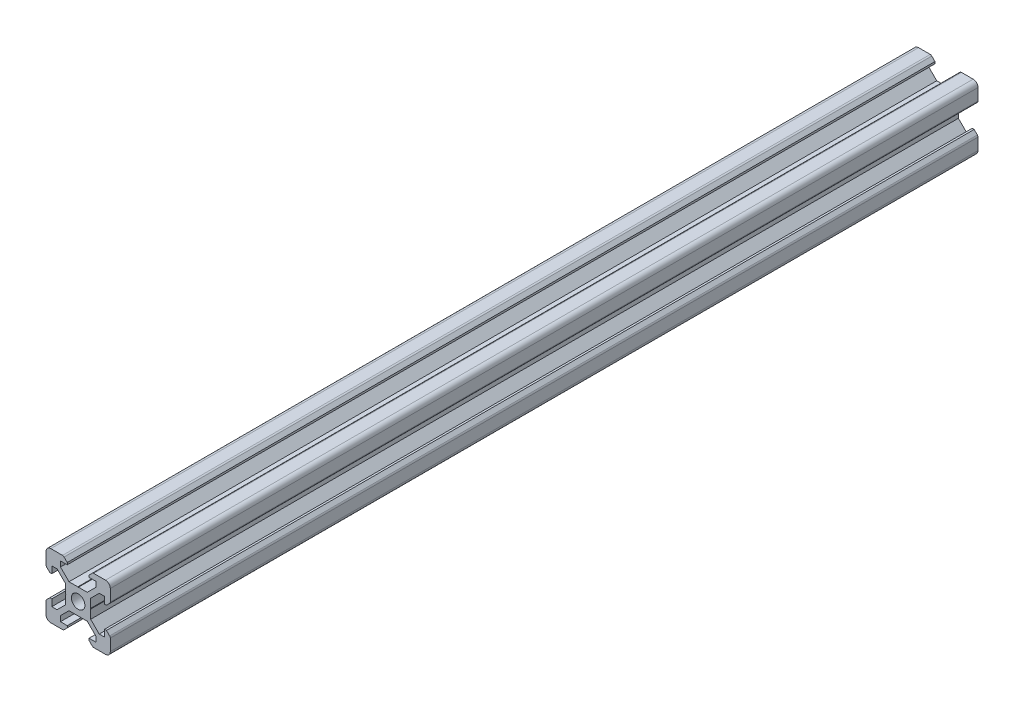
SolidWorks part; units mm, degrees
ref_plane "Front" through (0, 0, 0) normal (0, 0, 1) x (1, 0, 0)
ref_plane "Top" through (0, 0, 0) normal (0, 1, 0) x (1, 0, 0)
ref_plane "Right" through (0, 0, 0) normal (1, 0, 0) x (0, 0, -1)
sketch "Sketch1" plane through (0, 0, 0) normal (0, 0, 1) x (1, 0, 0)
  line L0 (-8.5, 10) -> (-10, 8.5) construction
  line L1 (-8.5, 10) -> (-4.8628, 10)
  line L2 (-10, 8.5) -> (-10, 4.8628)
  line L3 (-8.5, -10) -> (-4.8628, -10)
  line L4 (10, 8.5) -> (10, 4.8628)
  line L5 (-10, 10) -> (10, -10) construction
  line L6 (-10, -10) -> (10, 10) construction
  line L7 (-5.5, -8.2) -> (-3.3865, -8.2)
  line L8 (-8.2, -5.5) -> (-8.2, -3.3865)
  line L9 (-5.5, 8.2) -> (-3.3865, 8.2)
  line L10 (8.2, -5.5) -> (8.2, -3.3865)
  line L11 (-3.9005, 2.8395) -> (-6.561, 5.5)
  line L12 (-6.561, 5.5) -> (-8.2, 5.5)
  line L13 (-2.8395, -3.9005) -> (-0.1, -3.9005)
  line L14 (-3.9005, -2.8395) -> (-3.9005, -0.1)
  line L15 (-2.8395, 3.9005) -> (-0.1, 3.9005)
  line L16 (3.9005, -2.8395) -> (3.9005, -0.1)
  line L17 (-8.2, 3.3865) -> (-8.81, 3.3865)
  line L18 (-8.81, 3.3865) -> (-9.7976, 4.3741)
  line L19 (8.5, 10) -> (10, 8.5) construction
  line L20 (-2.8395, 3.9005) -> (-5.5, 6.561)
  line L21 (-5.5, 6.561) -> (-5.5, 8.2)
  line L22 (-3.3865, 8.2) -> (-3.3865, 8.81)
  line L23 (-3.3865, 8.81) -> (-4.3741, 9.7976)
  line L24 (0, 24.069) -> (0, -33.8154) construction
  line L25 (3.3865, 8.81) -> (4.3741, 9.7976)
  line L26 (3.3865, 8.2) -> (3.3865, 8.81)
  line L27 (5.5, 6.561) -> (5.5, 8.2)
  line L28 (2.8395, 3.9005) -> (5.5, 6.561)
  line L29 (3.3865, 8.2) -> (5.5, 8.2)
  line L30 (4.8628, 10) -> (8.5, 10)
  line L31 (-0.1, 3.9005) -> (0, 3.8005)
  line L32 (0.1, 3.9005) -> (0, 3.8005)
  line L33 (0.1, 3.9005) -> (2.8395, 3.9005)
  line L34 (25.9287, 0) -> (-28.3459, 0) construction
  line L35 (-0.1, -3.9005) -> (0, -3.8005)
  line L36 (0.1, -3.9005) -> (0, -3.8005)
  line L37 (0.1, -3.9005) -> (2.8395, -3.9005)
  line L38 (-3.9005, 0.1) -> (-3.8005, 0)
  line L39 (-3.8005, 0) -> (-3.9005, -0.1)
  line L40 (-3.9005, 0.1) -> (-3.9005, 2.8395)
  line L41 (3.9005, 0.1) -> (3.8005, 0)
  line L42 (3.8005, 0) -> (3.9005, -0.1)
  line L43 (3.9005, 0.1) -> (3.9005, 2.8395)
  line L44 (8.81, 3.3865) -> (9.7976, 4.3741)
  line L45 (8.2, 3.3865) -> (8.81, 3.3865)
  line L46 (6.561, 5.5) -> (8.2, 5.5)
  line L47 (3.9005, 2.8395) -> (6.561, 5.5)
  line L48 (2.8395, -3.9005) -> (5.5, -6.561)
  line L49 (3.9005, -2.8395) -> (6.561, -5.5)
  line L50 (-2.8395, -3.9005) -> (-5.5, -6.561)
  line L51 (-3.9005, -2.8395) -> (-6.561, -5.5)
  line L52 (6.561, -5.5) -> (8.2, -5.5)
  line L53 (-6.561, -5.5) -> (-8.2, -5.5)
  line L54 (-8.81, -3.3865) -> (-9.7976, -4.3741)
  line L55 (-8.2, -3.3865) -> (-8.81, -3.3865)
  line L56 (8.81, -3.3865) -> (9.7976, -4.3741)
  line L57 (8.2, -3.3865) -> (8.81, -3.3865)
  line L58 (8.2, 3.3865) -> (8.2, 5.5)
  line L59 (10, -4.8628) -> (10, -8.5)
  line L60 (-8.2, 3.3865) -> (-8.2, 5.5)
  line L61 (-10, -4.8628) -> (-10, -8.5)
  line L62 (-3.3865, -8.81) -> (-4.3741, -9.7976)
  line L63 (-3.3865, -8.2) -> (-3.3865, -8.81)
  line L64 (3.3865, -8.81) -> (4.3741, -9.7976)
  line L65 (3.3865, -8.2) -> (3.3865, -8.81)
  line L66 (-5.5, -6.561) -> (-5.5, -8.2)
  line L67 (5.5, -6.561) -> (5.5, -8.2)
  line L68 (3.3865, -8.2) -> (5.5, -8.2)
  line L69 (4.8628, -10) -> (8.5, -10)
  circle A0 centre (0, 0) radius 2.1
  arc A1 (-8.5, 10) -> (-10, 8.5) centre (-8.5, 8.5) ccw
  arc A2 (10, 8.5) -> (8.5, 10) centre (8.5, 8.5) ccw
  arc A3 (-4.3741, 9.7976) -> (-4.8628, 10) centre (-4.8628, 9.3088) ccw
  arc A4 (4.8628, 10) -> (4.3741, 9.7976) centre (4.8628, 9.3088) ccw
  arc A5 (-8.5, -10) -> (-10, -8.5) centre (-8.5, -8.5) cw
  arc A6 (9.7976, 4.3741) -> (10, 4.8628) centre (9.3088, 4.8628) ccw
  arc A7 (-10, 4.8628) -> (-9.7976, 4.3741) centre (-9.3088, 4.8628) ccw
  arc A8 (-10, -4.8628) -> (-9.7976, -4.3741) centre (-9.3088, -4.8628) cw
  arc A9 (9.7976, -4.3741) -> (10, -4.8628) centre (9.3088, -4.8628) cw
  arc A10 (10, -8.5) -> (8.5, -10) centre (8.5, -8.5) cw
  arc A11 (-4.3741, -9.7976) -> (-4.8628, -10) centre (-4.8628, -9.3088) cw
  arc A12 (4.8628, -10) -> (4.3741, -9.7976) centre (4.8628, -9.3088) cw
  point P17 (-9.25, 9.25)
  point P21 (9.25, 9.25)
  dimension "D2" = 4.2
  dimension "D4" = 1.5
  dimension "D3" = 20
  dimension "D5" = 0.529
  dimension "D6" = 6.773
  dimension "D7" = 90
  dimension "D8" = 11
  dimension "D9" = 0.61
  dimension "D10" = 0.1
  dimension "D11" = 0.1
  dimension "D12" = 0.1
  dimension "D13" = 0.1
  dimension "D14" = 5.679
  dimension "D15" = 1.639
  dimension "D16" = 1.8
  dimension "D17" = 90
  dimension "D18" = 6.773
  dimension "D19" = 90
extrude "Boss-Extrude1" add sketch "Sketch1" along normal blind 270
